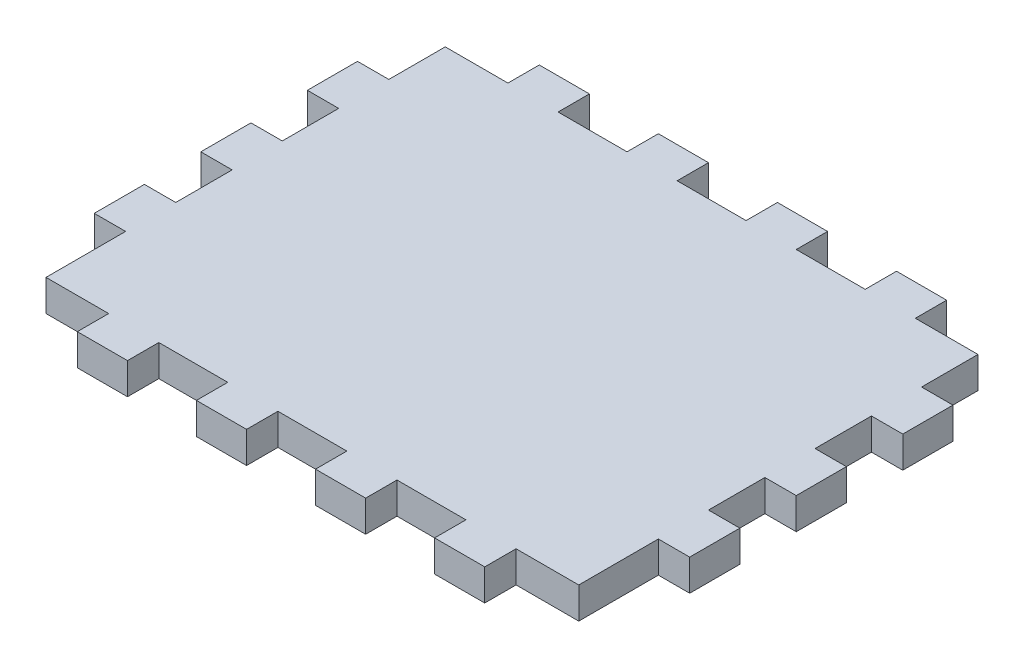
SolidWorks part; units mm, degrees
ref_plane "Front Plane" through (0, 0, 0) normal (0, 0, 1) x (1, 0, 0)
ref_plane "Top Plane" through (0, 0, 0) normal (0, 1, 0) x (1, 0, 0)
ref_plane "Right Plane" through (0, 0, 0) normal (1, 0, 0) x (0, 0, -1)
sketch "Sketch1" plane through (0, 0, 0) normal (0, 1, 0) x (1, 0, 0)
  line L1 (-44.2573, 24.2851) -> (-34.2573, 24.2851)
  line L2 (-44.2573, 24.2851) -> (-44.2573, 15.2851)
  line L3 (30.7427, -39.4149) -> (40.7427, -39.4149)
  line L4 (40.7427, 24.2851) -> (40.7427, 15.2851)
  line L5 (11.7427, -39.4149) -> (22.7427, -39.4149)
  line L6 (-34.2573, 24.2851) -> (-34.2573, 29.2851)
  line L7 (-34.2573, 29.2851) -> (-26.2573, 29.2851)
  line L8 (-26.2573, 24.2851) -> (-26.2573, 29.2851)
  line L9 (-15.2573, 24.2851) -> (-15.2573, 29.2851)
  line L10 (-15.2573, 29.2851) -> (-7.2573, 29.2851)
  line L11 (-7.2573, 24.2851) -> (-7.2573, 29.2851)
  line L12 (-7.2573, -39.4149) -> (3.7427, -39.4149)
  line L13 (3.7427, 24.2851) -> (3.7427, 29.2851)
  line L14 (3.7427, 29.2851) -> (11.7427, 29.2851)
  line L15 (11.7427, 24.2851) -> (11.7427, 29.2851)
  line L16 (-26.2573, -39.4149) -> (-15.2573, -39.4149)
  line L17 (22.7427, 24.2851) -> (22.7427, 29.2851)
  line L18 (22.7427, 29.2851) -> (30.7427, 29.2851)
  line L19 (30.7427, 24.2851) -> (30.7427, 29.2851)
  line L20 (30.7427, -39.4149) -> (30.7427, -44.4149)
  line L21 (-26.2573, 24.2851) -> (-15.2573, 24.2851)
  line L22 (-7.2573, 24.2851) -> (3.7427, 24.2851)
  line L23 (11.7427, 24.2851) -> (22.7427, 24.2851)
  line L24 (30.7427, 24.2851) -> (40.7427, 24.2851)
  line L25 (22.7427, -44.4149) -> (30.7427, -44.4149)
  line L26 (22.7427, -39.4149) -> (22.7427, -44.4149)
  line L27 (11.7427, -39.4149) -> (11.7427, -44.4149)
  line L28 (3.7427, -44.4149) -> (11.7427, -44.4149)
  line L29 (3.7427, -39.4149) -> (3.7427, -44.4149)
  line L30 (-7.2573, -39.4149) -> (-7.2573, -44.4149)
  line L31 (-15.2573, -44.4149) -> (-7.2573, -44.4149)
  line L32 (-15.2573, -39.4149) -> (-15.2573, -44.4149)
  line L33 (-26.2573, -39.4149) -> (-26.2573, -44.4149)
  line L34 (-34.2573, -44.4149) -> (-26.2573, -44.4149)
  line L35 (-34.2573, -39.4149) -> (-34.2573, -44.4149)
  line L36 (-44.2573, -39.4149) -> (-34.2573, -39.4149)
  line L38 (-44.2573, 15.2851) -> (-49.2573, 15.2851)
  line L39 (40.7427, -26.7149) -> (40.7427, -39.4149)
  line L40 (-44.2573, 7.2851) -> (-49.2573, 7.2851)
  line L41 (-49.2573, 15.2851) -> (-49.2573, 7.2851)
  line L42 (40.7427, 7.2851) -> (45.7427, 7.2851)
  line L43 (45.7427, 15.2851) -> (45.7427, 7.2851)
  line L44 (40.7427, 15.2851) -> (45.7427, 15.2851)
  line L45 (-44.2573, -1.7149) -> (-49.2573, -1.7149)
  line L47 (-44.2573, -9.7149) -> (-49.2573, -9.7149)
  line L48 (-49.2573, -1.7149) -> (-49.2573, -9.7149)
  line L49 (-44.2573, -18.7149) -> (-49.2573, -18.7149)
  line L51 (-44.2573, -26.7149) -> (-49.2573, -26.7149)
  line L52 (-49.2573, -18.7149) -> (-49.2573, -26.7149)
  line L53 (40.7427, -1.7149) -> (45.7427, -1.7149)
  line L54 (45.7427, -1.7149) -> (45.7427, -9.7149)
  line L55 (40.7427, -9.7149) -> (45.7427, -9.7149)
  line L56 (40.7427, -18.7149) -> (45.7427, -18.7149)
  line L57 (45.7427, -18.7149) -> (45.7427, -26.7149)
  line L58 (40.7427, -26.7149) -> (45.7427, -26.7149)
  line L59 (-44.2573, -26.7149) -> (-44.2573, -39.4149)
  line L60 (-44.2573, -9.7149) -> (-44.2573, -18.7149)
  line L61 (-44.2573, 7.2851) -> (-44.2573, -1.7149)
  line L62 (40.7427, 7.2851) -> (40.7427, -1.7149)
  line L63 (40.7427, -9.7149) -> (40.7427, -18.7149)
  point P42 (-108.3514, 28.1952)
  dimension "D2" = 8
  dimension "D3" = 3
  dimension "D5" = 11
  dimension "D6" = 9
  dimension "D7" = 9
  dimension "D8" = 95
  dimension "D9" = 8
  dimension "D10" = 5
  dimension "D11" = 10
  dimension "D12" = 12.7
  dimension "D1" = 4
  dimension "D4" = 3
extrude "Boss-Extrude1" add sketch "Sketch1" along normal blind 5
